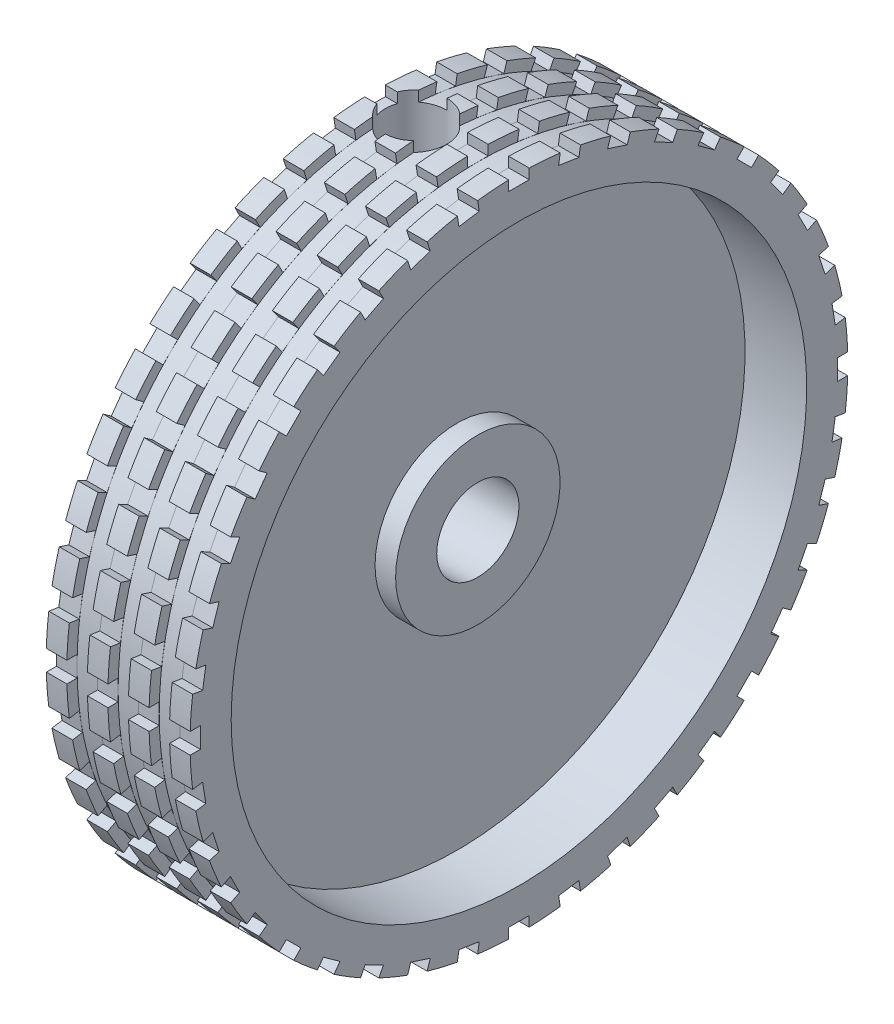
SolidWorks part; units mm, degrees
ref_plane "Front Plane" through (0, 0, 0) normal (0, 0, 1) x (1, 0, 0)
ref_plane "Top Plane" through (0, 0, 0) normal (0, 1, 0) x (1, 0, 0)
ref_plane "Right Plane" through (0, 0, 0) normal (1, 0, 0) x (0, 0, -1)
sketch "Sketch1" plane through (0, 0, 0) normal (0, 0, 1) x (1, 0, 0)
  line L0 (0, 0) -> (11.7557, 0) construction
  line L1 (0, 2) -> (0, 16)
  line L2 (0, 16) -> (7, 16)
  line L3 (7, 16) -> (7, 14)
  line L4 (7, 14) -> (4, 14)
  line L5 (4, 14) -> (4, 4)
  line L6 (4, 4) -> (5, 4)
  line L7 (5, 4) -> (5, 2)
  line L8 (0, 2) -> (5, 2)
  line L9 (0, 0) -> (0, 24.9657) construction
  dimension "D1" = 7
  dimension "D2" = 32
  dimension "D3" = 28
  dimension "D4" = 8
  dimension "D5" = 4
  dimension "D6" = 5
  dimension "D7" = 4
revolve "Revolve1" add sketch "Sketch1" angle 360 about L0
sketch "Sketch2" plane through (0, 0, 0) normal (0, 0, 1) x (1, 0, 0)
  line L0 (0, 0) -> (12.518, 0) construction
  line L1 (0, 0) -> (0, 17.4206) construction
  line L2 (2, 16) -> (3.5, 16)
  line L3 (3.5, 16) -> (3.5, 11.5)
  line L4 (3.5, 11.5) -> (2.9, 11.5)
  line L5 (2.9, 11.5) -> (2.9, 0)
  line L6 (2.9, 0) -> (2, 0)
  line L7 (2, 0) -> (2, 16)
  line L8 (1.1, 0) -> (1.1, 18.6849) construction
  line L9 (7, 16) -> (0, 16) construction
  dimension "D1" = 3.6
  dimension "D2" = 2
  dimension "D3" = 1.5
  dimension "D4" = 4.5
  dimension "D5" = 0.9
revolve "Cut-Revolve2" cut sketch "Sketch2" angle 360 about L7
sketch "Sketch3" plane through (0, 0, 0) normal (0, 0, 1) x (1, 0, 0)
  line L0 (0, 0) -> (22.2697, 0) construction
  line L1 (7, 16) -> (3.4999, 16) construction
  line L2 (5, 16) -> (6, 16)
  line L3 (5, 16) -> (5, 15.5)
  line L4 (5, 15.5) -> (6, 15.5)
  line L5 (6, 16) -> (6, 15.5)
  line L6 (7, -16) -> (7, 16) construction
  dimension "D1" = 0.5
  dimension "D2" = 1
  dimension "D3" = 1
revolve "Cut-Revolve3" cut sketch "Sketch3" angle 360 about L0
sketch "Sketch6" plane through (0, 0, 0) normal (-1, 0, 0) x (0, 0, 1)
  line L0 (0, 0) -> (0, 24.9445) construction
  line L1 (0, 0) -> (34.5481, 0) construction
  line L3 (-0.5, 16.5) -> (0.5, 16.5)
  line L4 (-0.5, 16.5) -> (-0.5, 15.5)
  line L5 (-0.5, 15.5) -> (0.5, 15.5)
  line L6 (0.5, 16.5) -> (0.5, 15.5)
  dimension "D1" = 1
  dimension "D2" = 1
  dimension "D3" = 15.5
extrude "Cut-Extrude2" cut sketch "Sketch6" against normal blind 10
pattern_circular "CirPattern1" count 40 over 360 about axis through (0, 0, 0) along (1, 0, 0) of "Cut-Extrude2"
pattern_linear "LPattern1" count 3 spacing 2 along (-1, 0, 0) of "Cut-Revolve3"
